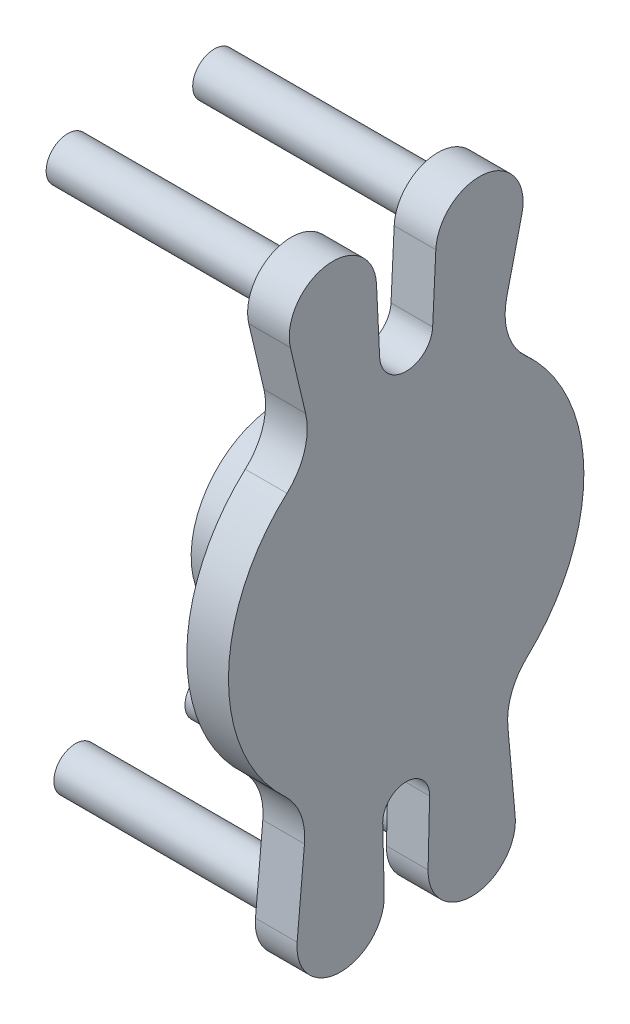
SolidWorks part; units mm, degrees
ref_plane "Front Plane" through (0, 0, 0) normal (0, 0, 1) x (1, 0, 0)
ref_plane "Top Plane" through (0, 0, 0) normal (0, 1, 0) x (1, 0, 0)
ref_plane "Right Plane" through (0, 0, 0) normal (1, 0, 0) x (0, 0, -1)
sketch "Sketch1" plane through (0, 0, 0) normal (0, 0, 1) x (1, 0, 0)
  line L0 (8.255, 0) -> (-8.255, 0) construction
  line L1 (25.4, 0) -> (-25.4, 0) construction
  line L2 (8.255, 0) -> (8.255, 18.542)
  line L3 (8.255, 18.542) -> (25.4, 18.542)
  line L4 (25.4, 18.542) -> (25.4, 0)
  line L5 (8.255, 0) -> (25.4, 0)
  point P4 (0, 0)
  point P8 (0, 0)
  dimension "D1" = 16.51
  dimension "D2" = 50.8
  dimension "D3" = 18.542
revolve "Revolve1" add sketch "Sketch1" angle 360 about L5
sketch "Sketch2" plane through (8.255, 0, 0) normal (-1, 0, 0) x (0, 0, 1)
  circle A0 centre (0, 0) radius 3.7147
  dimension "D1" = 7.4295
extrude "Cut-Extrude1" cut sketch "Sketch2" against normal blind 8.5725
sketch "Sketch3" plane through (25.4, 0, 0) normal (1, 0, 0) x (0, 0, -1)
  line L0 (0, 0) -> (0, -54.7688) construction
  line L1 (38.1, -54.7688) -> (-38.1, -54.7688) construction
  line L2 (38.1, -54.7688) -> (38.1, 54.7687) construction
  line L3 (38.1, 54.7687) -> (-38.1, 54.7687) construction
  line L4 (-38.1, -54.7688) -> (-38.1, 54.7687) construction
  line L5 (38.1, -54.7688) -> (-38.1, 54.7687) construction
  line L6 (38.1, 54.7687) -> (-38.1, -54.7688) construction
  line L7 (0, 0) -> (0, 54.7687) construction
  line L8 (-20.7029, 39.4483) -> (-23.827, 52.7082)
  line L9 (-6.1066, 55.2052) -> (-5.4533, 41.7705)
  line L10 (20.7029, 39.4483) -> (23.827, 52.7082)
  line L11 (6.1066, 55.2052) -> (5.4533, 41.7705)
  line L12 (38.1, 0) -> (-38.1, 0) construction
  line L13 (-20.9334, -37.1994) -> (-22.4428, -53.963)
  line L14 (-4.5111, -54.5527) -> (-4.8246, -41.518)
  line L15 (4.5111, -54.5527) -> (4.8246, -41.518)
  line L16 (20.9334, -37.1994) -> (22.4428, -53.963)
  circle A0 centre (15.0812, 54.7687) radius 6.4452 construction
  circle A1 centre (-15.0812, 54.7687) radius 6.4452 construction
  circle A2 centre (-13.4938, -54.7688) radius 6.4452 construction
  arc A4 (24.927, -26.7666) -> (24.5427, 27.1194) centre (0, 0) ccw
  arc A5 (-24.5427, 27.1194) -> (-20.7029, 39.4483) centre (-33.0644, 36.5358) ccw
  arc A6 (-6.1066, 55.2052) -> (-23.827, 52.7082) centre (-15.0812, 54.7687) ccw
  arc A7 (23.827, 52.7082) -> (6.1066, 55.2052) centre (15.0812, 54.7687) ccw
  arc A8 (-5.4533, 41.7705) -> (5.4533, 41.7705) centre (0, 42.0357) ccw
  arc A9 (24.5427, 27.1194) -> (20.7029, 39.4483) centre (33.0644, 36.5358) cw
  arc A10 (-22.4428, -53.963) -> (-4.5111, -54.5527) centre (-13.4938, -54.7688) ccw
  arc A11 (4.5111, -54.5527) -> (22.4428, -53.963) centre (13.4938, -54.7687) ccw
  arc A12 (-24.927, -26.7666) -> (-20.9334, -37.1994) centre (-33.5822, -36.0605) cw
  arc A13 (-4.8246, -41.518) -> (4.8246, -41.518) centre (0, -41.402) cw
  arc A14 (24.927, -26.7666) -> (20.9334, -37.1994) centre (33.5822, -36.0605) ccw
  circle A15 centre (-13.4938, -54.7688) radius 8.9852 construction
  arc A16 (-24.5427, 27.1194) -> (-24.927, -26.7666) centre (0, 0) ccw
  circle A17 centre (15.0812, 54.7687) radius 8.9852 construction
  circle A18 centre (-15.0812, 54.7687) radius 8.9852 construction
  point P0 (0, 0)
  point P6 (0, 0)
  point P39 (0, 0)
  dimension "D3" = 26.9875
  dimension "D5" = 9.0222
  dimension "D4" = 12.8905
  dimension "D7" = 73.152
  dimension "D9" = 12.7
  dimension "D12" = 5.4597
  dimension "D14" = 12.7
  dimension "D15" = 4.826
  dimension "D17" = 13.0347
  dimension "D1" = 109.5375
  dimension "D2" = 76.2
  dimension "D6" = 30.1625
  dimension "D10" = 13.2598
  dimension "D11" = 13.4347
  dimension "D16" = 16.7635
  dimension "D8" = 2.54
  dimension "D13" = 2.54
extrude "Boss-Extrude1" add sketch "Sketch3" along normal blind 8.5725
sketch "Sketch4" plane through (25.4, 0, 0) normal (-1, 0, 0) x (0, 0, 1)
  circle A0 centre (-15.0812, 54.7687) radius 6.4452 construction
  circle A1 centre (-15.0812, 54.7687) radius 6.4452 construction
  circle A2 centre (15.0812, 54.7687) radius 6.4452 construction
  circle A3 centre (15.0812, 54.7687) radius 6.4452 construction
  circle A4 centre (13.4938, -54.7688) radius 6.4452 construction
  circle A5 centre (13.4938, -54.7688) radius 6.4452 construction
  circle A6 centre (-13.4938, -54.7687) radius 6.4452 construction
  circle A7 centre (-15.0812, 54.7687) radius 4.45
  circle A8 centre (15.0812, 54.7687) radius 4.45
  circle A9 centre (-13.4938, -54.7687) radius 4.45
  circle A10 centre (13.4938, -54.7688) radius 4.45
  dimension "D1" = 12.8905
  dimension "D2" = 8.9
extrude "Boss-Extrude3" add sketch "Sketch4" along normal blind 46
